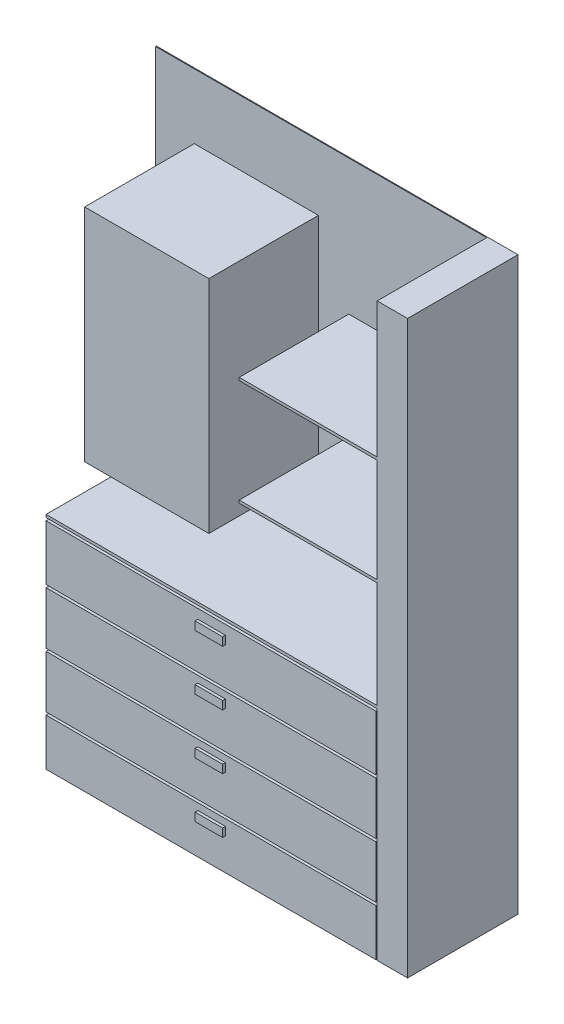
SolidWorks part; units mm, degrees
ref_plane "Front Plane" through (0, 0, 0) normal (0, 0, 1) x (1, 0, 0)
ref_plane "Top Plane" through (0, 0, 0) normal (0, 1, 0) x (1, 0, 0)
ref_plane "Right Plane" through (0, 0, 0) normal (1, 0, 0) x (0, 0, -1)
sketch "Sketch1" plane through (0, 0, 0) normal (0, 0, 1) x (1, 0, 0)
  line L1 (-655, 1035) -> (655, 1035)
  line L2 (-655, 1035) -> (-655, -1035)
  line L3 (-655, -1035) -> (655, -1035)
  line L4 (655, 1035) -> (655, -1035)
  line L5 (-655, 1035) -> (655, -1035) construction
  line L6 (-655, -1035) -> (655, 1035) construction
  point P0 (0, 0)
  dimension "D1" = 1310
  dimension "D2" = 2070
extrude "Boss-Extrude1" add sketch "Sketch1" along normal blind 400
sketch "Sketch2" plane through (0, 0, 400) normal (0, 0, 1) x (1, 0, 0)
  line L0 (-655, -1035) -> (655, -1035) construction
  line L1 (545, -235) -> (-655, -235)
  line L2 (545, -235) -> (545, 165)
  line L3 (545, 165) -> (-655, 165)
  line L4 (-655, -235) -> (-655, 165)
  line L6 (-655, 1035) -> (-655, -1035) construction
  dimension "D1" = 400
  dimension "D2" = 1200
  dimension "D3" = 800
extrude "Cut-Extrude2" cut sketch "Sketch2" against normal offset from surface (397 mm away) 3 up to face at (0, 0, 0)
sketch "Sketch5" plane through (0, 0, 400) normal (0, 0, 1) x (1, 0, 0)
  line L8 (545, -245) -> (-655, -245)
  line L9 (545, -245) -> (545, -255)
  line L10 (545, -255) -> (-655, -255)
  line L11 (-655, -245) -> (-655, -255)
  line L12 (-655, 1035) -> (-655, 165) construction
  line L13 (545, -235) -> (-655, -235) construction
  line L14 (655, -1035) -> (655, 1035) construction
  dimension "D1" = 10
  dimension "D2" = 10
  dimension "D3" = 110
extrude "Cut-Extrude5" cut sketch "Sketch5" against normal offset from surface (397 mm away) 3 up to face at (0, 0, 0)
sketch "Sketch6" plane through (0, 0, 400) normal (0, 0, 1) x (1, 0, 0)
  line L1 (545, -455) -> (-655, -455)
  line L2 (545, -455) -> (545, -465)
  line L3 (545, -465) -> (-655, -465)
  line L4 (-655, -455) -> (-655, -465)
  line L5 (-655, -255) -> (-655, -1035) construction
  line L6 (-655, -255) -> (545, -255) construction
  line L7 (655, -1035) -> (655, 1035) construction
  dimension "D1" = 10
  dimension "D2" = 200
  dimension "D3" = 110
extrude "Cut-Extrude6" cut sketch "Sketch6" against normal offset from surface (397 mm away) 3 up to face at (0, 0, 0)
pattern_linear "LPattern2" count 3 spacing 200 along (0, -1, 0) of "Cut-Extrude6"
sketch "Sketch9" plane through (0, 0, 400) normal (0, 0, 1) x (1, 0, 0)
  line L0 (545, -255) -> (-655, -255) construction
  line L1 (-105, -289.2371) -> (-5, -289.2371)
  line L2 (-105, -289.2371) -> (-105, -319.2371)
  line L3 (-105, -319.2371) -> (-5, -319.2371)
  line L4 (-5, -289.2371) -> (-5, -319.2371)
  point P6 (-55, -255)
  point P7 (-55, -289.2371)
  dimension "D1" = 100
  dimension "D2" = 30
extrude "Boss-Extrude2" add sketch "Sketch9" along normal blind 10
pattern_linear "LPattern3" count 4 spacing 200 along (0, -1, 0) of "Boss-Extrude2"
sketch "Sketch11" plane through (0, 0, 400) normal (0, 0, 1) x (1, 0, 0)
  line L0 (655, 1035) -> (-655, 1035) construction
  line L1 (655, -1035) -> (545, -1035)
  line L2 (655, -1035) -> (655, 1035)
  line L3 (655, 1035) -> (545, 1035)
  line L4 (545, -1035) -> (545, 1035)
  dimension "D1" = 110
extrude "Boss-Extrude3" add sketch "Sketch11" against normal up to surface (400 mm away) separate body up to face at (0, 0, 0)
sketch "Sketch12" plane through (0, 0, 400) normal (0, 0, 1) x (1, 0, 0)
  line L0 (545, 1035) -> (545, -1035) construction
  line L1 (545, 665) -> (45, 665)
  line L2 (545, 665) -> (545, 675)
  line L3 (545, 675) -> (45, 675)
  line L4 (45, 665) -> (45, 675)
  line L6 (545, 165) -> (-655, 165) construction
  dimension "D1" = 10
  dimension "D2" = 500
  dimension "D3" = 500
extrude "Cut-Extrude9" cut sketch "Sketch12" against normal offset from surface (397 mm away) 3 up to face at (0, 0, 0)
sketch "Sketch13" plane through (0, 0, 400) normal (0, 0, 1) x (1, 0, 0)
  line L1 (545, 165) -> (-655, 165)
  line L2 (545, 165) -> (545, 1035)
  line L3 (545, 1035) -> (-655, 1035)
  line L4 (-655, 165) -> (-655, 1035)
extrude "Cut-Extrude10" cut sketch "Sketch13" against normal offset from surface (397 mm away) 3 up to face at (0, 0, 0)
sketch "Sketch14" plane through (0, 0, 3) normal (0, 0, 1) x (1, 0, 0)
  line L0 (545, 1035) -> (545, -235) construction
  line L1 (545, 160) -> (45, 160)
  line L2 (545, 160) -> (545, 150)
  line L3 (545, 150) -> (45, 150)
  line L4 (45, 160) -> (45, 150)
  line L5 (545, -235) -> (-655, -235) construction
  dimension "D1" = 500
  dimension "D2" = 10
  dimension "D3" = 385
extrude "Boss-Extrude4" add sketch "Sketch14" along normal up to surface (397 mm away) up to face at (600, 0, 400)
pattern_linear "LPattern4" count 2 spacing 385 along (0, 1, 0) of "Boss-Extrude4"
sketch "Sketch16" plane through (0, 0, 400) normal (0, 0, 1) x (1, 0, 0)
  line L0 (-655, -1035) -> (655, -1035) construction
  line L1 (545, -255) -> (540, -255)
  line L2 (545, -255) -> (545, -1035)
  line L3 (545, -1035) -> (540, -1035)
  line L4 (540, -255) -> (540, -1035)
  dimension "D1" = 5
extrude "Cut-Extrude11" cut sketch "Sketch16" against normal offset from surface (397 mm away) 3 up to face at (0, 0, 0)
sketch "Sketch17" plane through (0, 0, 3) normal (0, 0, 1) x (1, 0, 0)
  line L1 (-515, 800) -> (-65, 800)
  line L2 (-515, 800) -> (-515, 0)
  line L3 (-515, 0) -> (-65, 0)
  line L4 (-65, 800) -> (-65, 0)
  line L5 (545, -235) -> (-655, -235) construction
  line L7 (-655, -235) -> (-655, 1035) construction
  dimension "D1" = 450
  dimension "D2" = 800
  dimension "D3" = 235
  dimension "D4" = 140
extrude "Boss-Extrude5" add sketch "Sketch17" along normal up to surface (397 mm away) up to face at (283.75, 113.75, 400)
